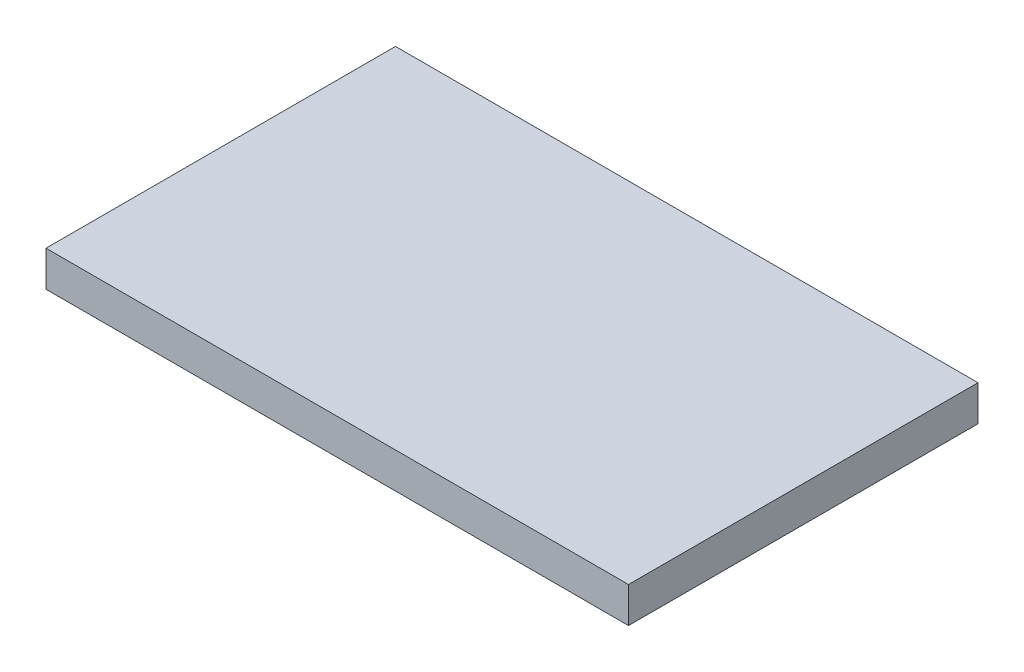
SolidWorks part; units mm, degrees
ref_plane "Front Plane" through (0, 0, 0) normal (0, 0, 1) x (1, 0, 0)
ref_plane "Top Plane" through (0, 0, 0) normal (0, 1, 0) x (1, 0, 0)
ref_plane "Right Plane" through (0, 0, 0) normal (1, 0, 0) x (0, 0, -1)
sketch "Sketch1" plane through (0, 0, 0) normal (0, 1, 0) x (1, 0, 0)
  line L1 (-16.375, 9.825) -> (16.375, 9.825)
  line L2 (-16.375, 9.825) -> (-16.375, -9.825)
  line L3 (-16.375, -9.825) -> (16.375, -9.825)
  line L4 (16.375, 9.825) -> (16.375, -9.825)
  line L5 (-16.375, 9.825) -> (16.375, -9.825) construction
  line L6 (-16.375, -9.825) -> (16.375, 9.825) construction
  point P0 (0, 0)
  dimension "D1" = 19.65
  dimension "D2" = 32.75
extrude "Boss-Extrude1" add sketch "Sketch1" along normal blind 2
